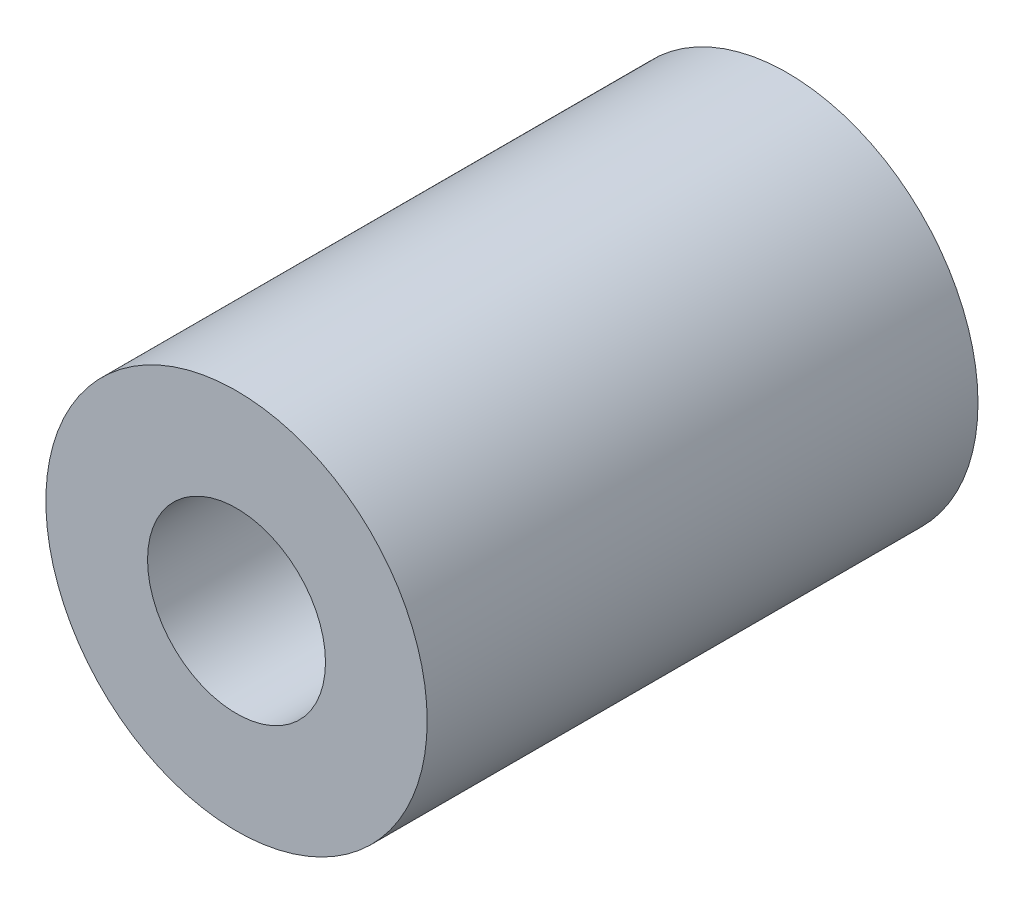
SolidWorks part; units mm, degrees
ref_plane "Front" through (0, 0, 0) normal (0, 0, 1) x (1, 0, 0)
ref_plane "Top" through (0, 0, 0) normal (0, 1, 0) x (1, 0, 0)
ref_plane "Right" through (0, 0, 0) normal (1, 0, 0) x (0, 0, -1)
sketch "Croquis1" plane through (0, 0, 0) normal (0, 0, 1) x (1, 0, 0)
  circle A0 centre (0, 0) radius 9
  circle A1 centre (0, 0) radius 4.2
  dimension "D1" = 8.4
  dimension "D2" = 18
extrude "Saliente-Extruir1" add sketch "Croquis1" along normal blind 26
